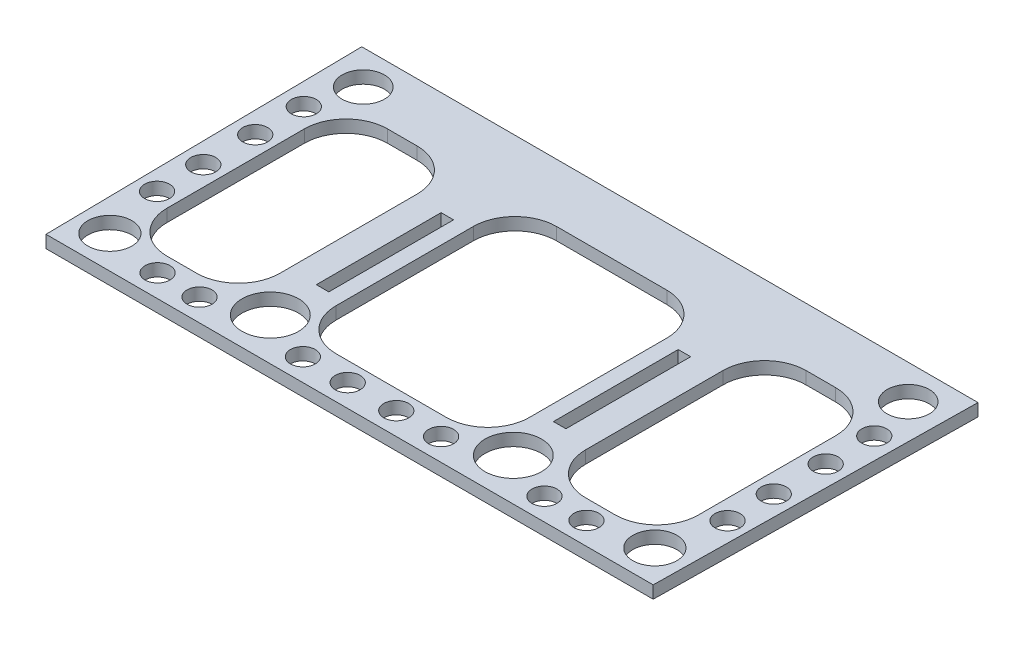
SolidWorks part; units mm, degrees
ref_plane "Front Plane" through (0, 0, 0) normal (0, 0, 1) x (1, 0, 0)
ref_plane "Top Plane" through (0, 0, 0) normal (0, 1, 0) x (1, 0, 0)
ref_plane "Right Plane" through (0, 0, 0) normal (1, 0, 0) x (0, 0, -1)
sketch "Sketch1" plane through (0, 0, 0) normal (0, 1, 0) x (1, 0, 0)
  line L0 (-72.9864, 0) -> (72.9864, 0)
  line L1 (-72.9864, 0) -> (-74.075, 77)
  line L2 (-74.075, 77) -> (74.075, 77)
  line L3 (74.075, 77) -> (72.9864, 0)
  point P4 (0, 0)
  dimension "D1" = 89.19
  dimension "D2" = 89.19
  dimension "D3" = 148.15
  dimension "D4" = 77
extrude "Boss-Extrude1" add sketch "Sketch1" along normal blind 3
sketch "Sketch2" plane through (0, 3, 0) normal (0, 1, 0) x (1, 0, 0)
  line L0 (-74.075, 77) -> (-72.9864, 0) construction
  line L1 (-30, -70.8527) -> (30, -70.8527) construction
  line L2 (-30, -70.8527) -> (-30, 70.8527) construction
  line L3 (-30, 70.8527) -> (30, 70.8527) construction
  line L4 (30, -70.8527) -> (30, 70.8527) construction
  line L5 (-30, -70.8527) -> (30, 70.8527) construction
  line L6 (-30, 70.8527) -> (30, -70.8527) construction
  line L7 (-36.75, -82.8936) -> (36.75, -82.8936) construction
  line L8 (-36.75, -82.8936) -> (-36.75, 82.8936) construction
  line L9 (-36.75, 82.8936) -> (36.75, 82.8936) construction
  line L10 (36.75, -82.8936) -> (36.75, 82.8936) construction
  line L11 (-36.75, -82.8936) -> (36.75, 82.8936) construction
  line L12 (-36.75, 82.8936) -> (36.75, -82.8936) construction
  line L13 (-46.75, 63) -> (-53.8761, 63)
  line L14 (-36.75, 53) -> (-36.75, 20)
  line L15 (-46.75, 10) -> (-53.8761, 10)
  line L16 (-63.8761, 53) -> (-63.8761, 20)
  line L21 (-23.25, -65.2871) -> (23.25, -65.2871) construction
  line L22 (-23.25, -65.2871) -> (-23.25, 65.2871) construction
  line L23 (-23.25, 65.2871) -> (23.25, 65.2871) construction
  line L24 (23.25, -65.2871) -> (23.25, 65.2871) construction
  line L25 (-23.25, -65.2871) -> (23.25, 65.2871) construction
  line L26 (-23.25, 65.2871) -> (23.25, -65.2871) construction
  line L31 (30.7785, -8.8097) -> (-23.25, 64.0404) construction
  line L32 (30.7785, 53.8892) -> (-15.7215, -8.8097) construction
  line L33 (-13.25, 63) -> (0, 63)
  line L34 (-23.25, 53) -> (-23.25, 20)
  line L35 (-13.25, 10) -> (0, 10)
  line L36 (0, 63) -> (0, 10)
  line L37 (74.075, 77) -> (-74.075, 77) construction
  line L38 (-72.9864, 0) -> (72.9864, 0) construction
  arc A0 (-23.25, 20) -> (-13.25, 10) centre (-13.25, 20) ccw
  arc A1 (-13.25, 63) -> (-23.25, 53) centre (-13.25, 53) ccw
  arc A2 (-46.75, 63) -> (-36.75, 53) centre (-46.75, 53) cw
  arc A3 (-36.75, 20) -> (-46.75, 10) centre (-46.75, 20) cw
  arc A4 (-53.8761, 10) -> (-63.8761, 20) centre (-53.8761, 20) cw
  arc A5 (-53.8761, 63) -> (-63.8761, 53) centre (-53.8761, 53) ccw
  point P0 (0, 0)
  point P5 (0, 0)
  point P14 (0, 0)
  point P19 (7.5285, 22.5398)
  point P41 (-23.25, 63)
  point P44 (-36.75, 63)
  point P51 (-63.8761, 63)
  dimension "D7" = 10
  dimension "D1" = 60
  dimension "D2" = 6.75
  dimension "D3" = 6.75
  dimension "D4" = 10
  dimension "D5" = 14
  dimension "D6" = 10
extrude "Cut-Extrude1" cut sketch "Sketch2" against normal blind 10
mirror "Mirror1" about plane through (0, 0, 0) normal (1, 0, 0) of "Cut-Extrude1"
sketch "Sketch3" plane through (0, 3, 0) normal (0, 1, 0) x (1, 0, 0)
  line L0 (-1.65, 0) -> (1.65, 0) construction
  line L1 (-30, 52) -> (-27, 52)
  line L2 (-30, 52) -> (-30, 22)
  line L3 (-30, 22) -> (-27, 22)
  line L4 (-27, 52) -> (-27, 22)
  line L5 (0, -1.65) -> (0, 1.65) construction
  line L6 (30, 22) -> (27, 22)
  line L7 (27, 52) -> (27, 22)
  line L8 (30, 52) -> (27, 52)
  line L9 (30, 52) -> (30, 22)
  dimension "D1" = 30
  dimension "D2" = 22
  dimension "D3" = 3
  dimension "D4" = 54
extrude "Cut-Extrude2" cut sketch "Sketch3" against normal blind 10
sketch "Sketch4" plane through (0, 3, 0) normal (0, 1, 0) x (1, 0, 0)
  line L0 (0, -1.65) -> (0, 1.65) construction
  circle A0 centre (-65.5086, 68.7954) radius 5.073
  circle A3 centre (-68.5714, 57.5654) radius 3
  circle A4 centre (-68.5714, 45.8816) radius 3
  circle A5 centre (-68.5714, 33.4038) radius 3
  circle A6 centre (-68.5714, 22.2871) radius 3
  circle A8 centre (-51.5561, 5.3853) radius 3
  circle A9 centre (-41.4604, 5.3853) radius 3
  circle A10 centre (-16.6182, 5.3853) radius 3
  circle A11 centre (-5.8419, 5.3853) radius 3
  circle A12 centre (-65.5086, 7.8809) radius 5.2963
  circle A13 centre (-29.2095, 10.1496) radius 6.7957
  circle A14 centre (29.2095, 10.1496) radius 6.7957
  circle A15 centre (65.5086, 7.8809) radius 5.2963
  circle A16 centre (5.8419, 5.3853) radius 3
  circle A17 centre (16.6182, 5.3853) radius 3
  circle A18 centre (41.4604, 5.3853) radius 3
  circle A19 centre (51.5561, 5.3853) radius 3
  circle A20 centre (68.5714, 22.2871) radius 3
  circle A21 centre (68.5714, 33.4038) radius 3
  circle A22 centre (68.5714, 45.8816) radius 3
  circle A23 centre (68.5714, 57.5654) radius 3
  circle A26 centre (65.5086, 68.7954) radius 5.073
  dimension "D1" = 6
  dimension "D2" = 6
extrude "Cut-Extrude3" cut sketch "Sketch4" against normal blind 10
equation "\"D3@Sketch2\"=\"D2@Sketch2\""
